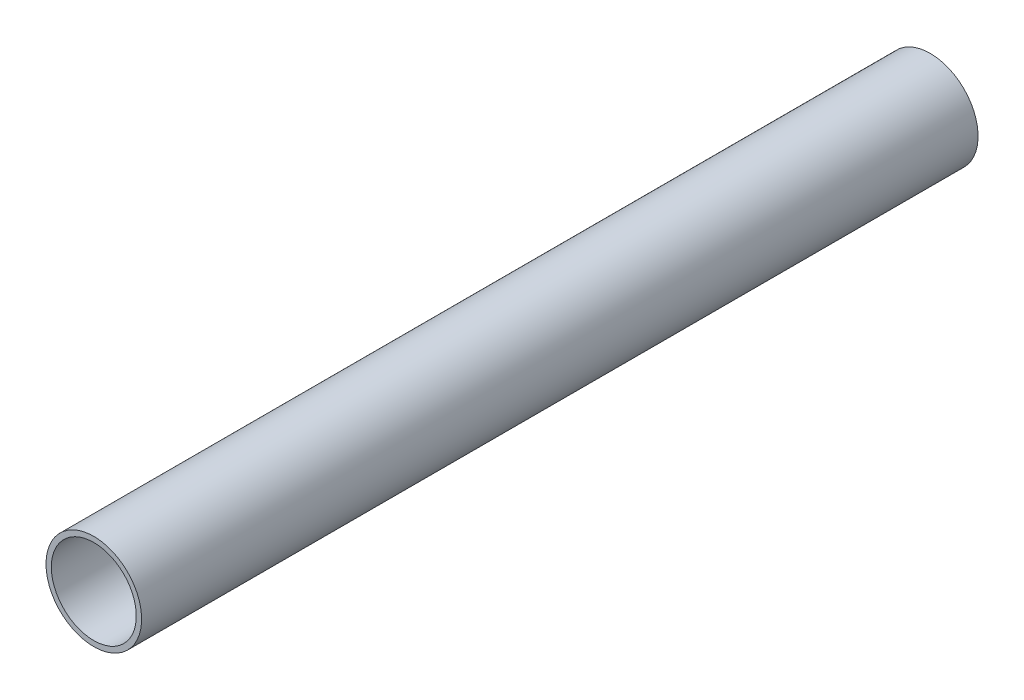
SolidWorks part; units mm, degrees
ref_plane "前视基准面" through (0, 0, 0) normal (0, 0, 1) x (1, 0, 0)
ref_plane "上视基准面" through (0, 0, 0) normal (0, 1, 0) x (1, 0, 0)
ref_plane "右视基准面" through (0, 0, 0) normal (1, 0, 0) x (0, 0, -1)
ref_plane "基准面4" through (0, 0, 0) normal (0, -1, 0) x (1, 0, 0)
sketch "草图1" plane through (0, 0, 0) normal (0, -1, 0) x (1, 0, 0)
  line L0 (50.8, -475) -> (57.15, -475)
  line L1 (57.15, -475) -> (57.15, 525)
  line L2 (57.15, 525) -> (50.8, 525)
  line L3 (50.8, 525) -> (50.8, -475)
  line L4 (0, 475) -> (0, -475) construction
  point P6 (0, 0)
revolve "旋转1" add sketch "草图1" angle 360 about L4
